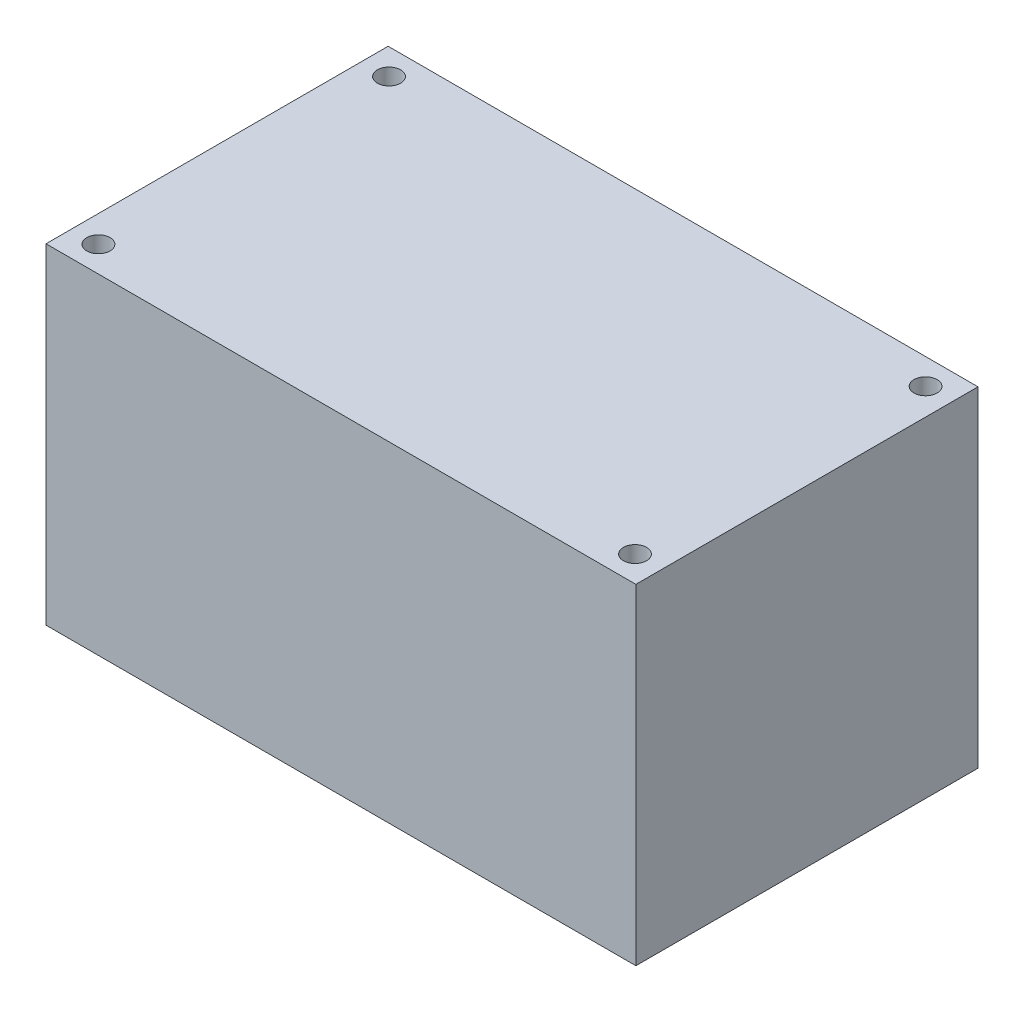
SolidWorks part; units mm, degrees
ref_plane "Front Plane" through (0, 0, 0) normal (0, 0, 1) x (1, 0, 0)
ref_plane "Top Plane" through (0, 0, 0) normal (0, 1, 0) x (1, 0, 0)
ref_plane "Right Plane" through (0, 0, 0) normal (1, 0, 0) x (0, 0, -1)
sketch "Sketch2" plane through (0, 0, 0) normal (0, 1, 0) x (1, 0, 0)
  line L1 (-31.75, 18.415) -> (31.75, 18.415)
  line L2 (-31.75, 18.415) -> (-31.75, -18.415)
  line L3 (-31.75, -18.415) -> (31.75, -18.415)
  line L4 (31.75, 18.415) -> (31.75, -18.415)
  line L5 (-31.75, 18.415) -> (31.75, -18.415) construction
  line L6 (-31.75, -18.415) -> (31.75, 18.415) construction
  point P0 (0, 0)
  dimension "D1" = 63.5
  dimension "D2" = 36.83
extrude "Boss-Extrude1" add sketch "Sketch2" along normal mid plane 35.56
sketch "Sketch3" plane through (0, 17.78, 0) normal (0, 1, 0) x (1, 0, 0)
  line L1 (-28.8808, 15.64) -> (28.8807, 15.64) construction
  line L2 (-28.8808, 15.64) -> (-28.8807, -15.6401) construction
  line L3 (-28.8807, -15.6401) -> (28.8808, -15.6401) construction
  line L4 (28.8807, 15.64) -> (28.8808, -15.6401) construction
  line L5 (-28.8808, 15.64) -> (28.8808, -15.6401) construction
  line L6 (-28.8807, -15.6401) -> (28.8807, 15.64) construction
  circle A0 centre (-28.8808, 15.64) radius 1.25
  circle A1 centre (28.8807, 15.64) radius 1.25
  circle A2 centre (28.8808, -15.6401) radius 1.25
  circle A3 centre (-28.8807, -15.6401) radius 1.25
  point P0 (0, 0)
  dimension "D3" = 2.5
  dimension "D1" = 57.7615
  dimension "D2" = 31.2801
extrude "Cut-Extrude1" cut sketch "Sketch3" against normal through all both and the other way through all
equation "\"AIRFRAME_OD\"= 3.142in"
equation "\"AIRFRAME_ID\"= 3.00in"
equation "\"FLAT_T\"= 0.125in"
equation "\"NOSE_EXP_L\"= 3.5in"
equation "\"NOSE_SHOULDER_L\"= 1.5in"
equation "\"MAIN_L\"= 30in"
equation "\"RECO_COUP_L\"= 6in"
equation "\"RECO_SWITCH_L\"= 1.5in"
equation "\"DROGUE_L\"= 14in"
equation "\"ATS_FORE_COUP_L\"= 4in"
equation "\"ATS_AFT_COUP_L\"= 2.5in"
equation "\"LOWER_L\"= 16in"
equation "\"FIN_N\"= 4"
equation "\"CR_AFT_X\"= 0.5in"
equation "\"CR_FORE_X\"= 6in"
equation "\"COUPLER_OD\"= 2.998in"
equation "\"COUPLER_ID\"= 2.875in"
equation "\"RECO_ROD_X\"= 1.5in"
equation "\"ATS_ROD_X\"= 2in"
equation "\"FIN_ROOT\"= 5in"
equation "\"FIN_X\"= 0.75in"
equation "\"MOTOR_OD\"= 2.25in"
equation "\"MOTOR_ID\"= 2.126in"
equation "\"MOTOR_L\"= 8in"
equation "\"MOTOR_LOWER_X\"= 0.5in"
equation "\"NOSE_CONE_L\"=14.5in"
equation "\"ATS_LIPO_L\" = 2.8in"
equation "\"ATS_LIPO_W\" = 0.625in"
equation "\"ATS_LIPO_H\" = 1.4in "
equation "\"ATS_STANDOFF_H\" = 10mm"
equation "\"ATS_STANDOFF_OD\" = 5.2mm"
equation "\"ATS_PCB_L\" = 2.5in"
equation "\"ATS_PCB_W\" = 1.45in"
equation "\"ATS_PCB_H\" = 1.2in"
equation "\"ATS_PCB_HOLESEP_W\" = 1.33in - 0.0985in"
equation "\"ATS_ALTI_L\" = 1.05in"
equation "\"ATS_ALTI_W\" = 0.7in"
equation "\"ATS_ALTI_H\" = 0.4in"
equation "\"D1@Sketch2\"=\"ATS_PCB_L\""
equation "\"D2@Sketch2\"=\"ATS_PCB_W\""
equation "\"D1@Boss-Extrude1\"=\"ATS_LIPO_H\""
equation "\"D2@Sketch3\"=\"ATS_PCB_HOLESEP_W\""
